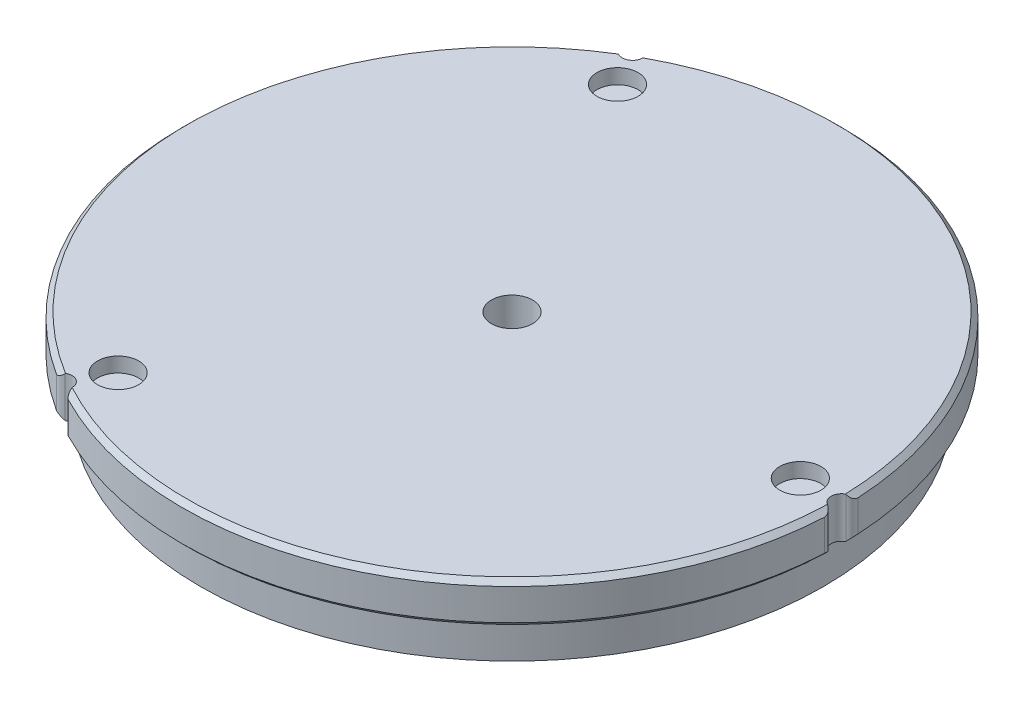
SolidWorks part; units mm, degrees
ref_plane "Front Plane" through (0, 0, 0) normal (0, 0, 1) x (1, 0, 0)
ref_plane "Top Plane" through (0, 0, 0) normal (0, 1, 0) x (1, 0, 0)
ref_plane "Right Plane" through (0, 0, 0) normal (1, 0, 0) x (0, 0, -1)
sketch "Sketch1" plane through (0, 0, 0) normal (0, 1, 0) x (1, 0, 0)
  circle A0 centre (0, 0) radius 50.8
  dimension "D1" = 101.6
extrude "Boss-Extrude1" add sketch "Sketch1" along normal blind 6.35
sketch "Sketch2" plane through (0, 6.35, 0) normal (0, 1, 0) x (1, 0, 0)
  line L0 (0, 0) -> (44.45, 0) construction
  line L1 (0, 0) -> (-22.225, 38.4948) construction
  line L2 (0, 0) -> (-22.225, -38.4948) construction
  circle A0 centre (0, 0) radius 44.45 construction
  circle A1 centre (-22.225, -38.4948) radius 3.175
  circle A2 centre (-22.225, 38.4948) radius 3.175
  circle A3 centre (44.45, 0) radius 3.175
  dimension "D1" = 88.9
  dimension "D4" = 6.35
  dimension "D2" = 120
  dimension "D3" = 120
extrude "Cut-Extrude1" cut sketch "Sketch2" against normal blind 2.286
sketch "Sketch3" plane through (0, 6.35, 0) normal (0, 1, 0) x (1, 0, 0)
  circle A0 centre (0, 0) radius 3.175
  dimension "D1" = 6.35
extrude "Cut-Extrude2" cut sketch "Sketch3" against normal through all both and the other way through all
sketch "Sketch4" plane through (0, 0, 0) normal (0, -1, 0) x (1, 0, 0)
  line L0 (0, 0) -> (44.45, 0) construction
  line L1 (0, 0) -> (-22.225, -38.4948) construction
  line L2 (0, 0) -> (-22.225, 38.4948) construction
  circle A0 centre (50.8, 0) radius 1.5875
  circle A1 centre (0, 0) radius 50.8 construction
  circle A2 centre (-25.4, 43.9941) radius 1.5875
  circle A3 centre (-25.4, -43.9941) radius 1.5875
  dimension "D1" = 3.175
extrude "Cut-Extrude3" cut sketch "Sketch4" against normal through all
chamfer "Chamfer1" distance 0.762 angle 45 6 edges at (25.4, 6.35, 43.9941) (25.4, 0, 43.9941) (-50.8, 0, 0) (-50.8, 6.35, 0) (25.4, 6.35, -43.9941) (25.4, 0, -43.9941)
fillet "Fillet1" radius 1.27 6 edges at (-24.013, 3.175, 44.7663) (-26.7622, 3.175, 43.179) (50.7752, 3.175, -1.5873) (50.7752, 3.175, 1.5873) (-24.013, 3.175, -44.7663) (-26.7622, 3.175, -43.179)
sketch "Sketch5" plane through (0, 0, 0) normal (0, -1, 0) x (1, 0, 0)
  circle A0 centre (0, 0) radius 46
  circle A1 centre (0, 0) radius 48
  dimension "D1" = 92
  dimension "D2" = 96
extrude "Boss-Extrude2" add sketch "Sketch5" along normal blind 6.35
